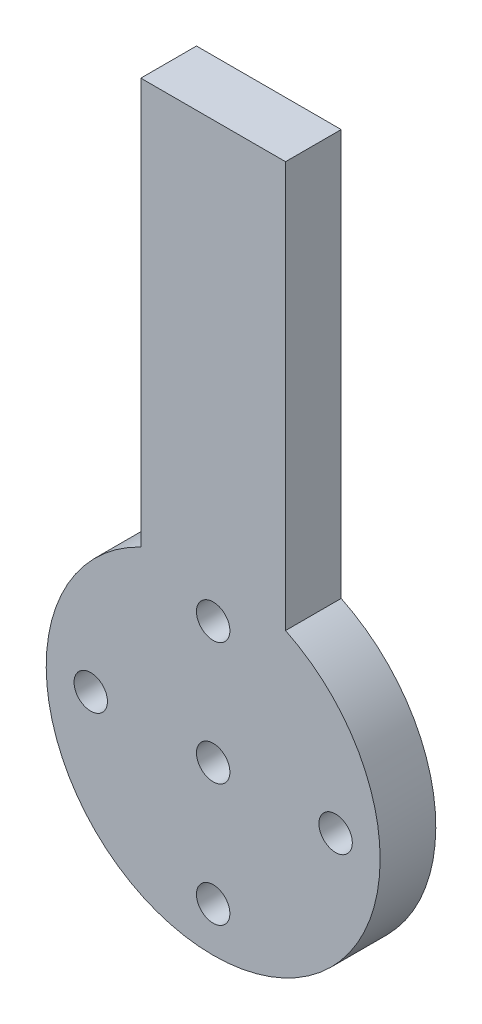
SolidWorks part; units mm, degrees
ref_plane "前视基准面" through (0, 0, 0) normal (0, 0, 1) x (1, 0, 0)
ref_plane "上视基准面" through (0, 0, 0) normal (0, 1, 0) x (1, 0, 0)
ref_plane "右视基准面" through (0, 0, 0) normal (1, 0, 0) x (0, 0, -1)
sketch "草图1" plane through (0, 0, 0) normal (0, 0, 1) x (1, 0, 0)
  line L0 (2468.8079, 4706.4663) -> (2468.8079, 4742.9478)
  line L1 (2481.8079, 4742.9478) -> (2481.8079, 4706.4663)
  line L9 (2468.8079, 4742.9478) -> (2481.8079, 4742.9478)
  circle A0 centre (2475.3079, 4692.9478) radius 1.5
  circle A1 centre (2464.3079, 4692.9478) radius 1.5
  circle A2 centre (2486.3079, 4692.9478) radius 1.5
  circle A3 centre (2475.3079, 4703.9478) radius 1.5
  circle A4 centre (2475.3079, 4681.9478) radius 1.5
  arc A5 (2468.8079, 4706.4663) -> (2481.8079, 4706.4663) centre (2475.3079, 4692.9478) ccw
extrude "凸台-拉伸1" add sketch "草图1" along normal blind 5
